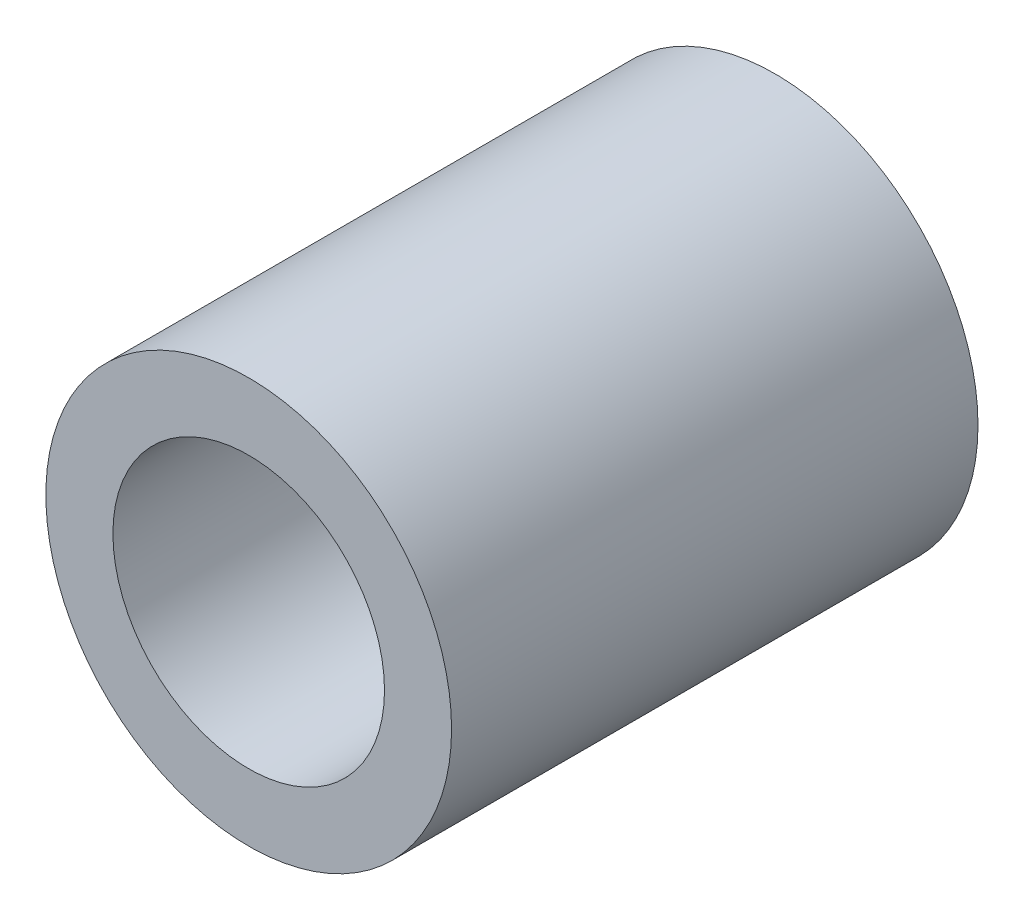
SolidWorks part; units mm, degrees
ref_plane "Alzado" through (0, 0, 0) normal (0, 0, 1) x (1, 0, 0)
ref_plane "Planta" through (0, 0, 0) normal (0, 1, 0) x (1, 0, 0)
ref_plane "Vista lateral" through (0, 0, 0) normal (1, 0, 0) x (0, 0, -1)
sketch "Croquis1" plane through (0, 0, 0) normal (0, 0, 1) x (1, 0, 0)
  circle A0 centre (0, 0) radius 4.05
  circle A1 centre (0, 0) radius 6.05
  dimension "D1" = 8.1
  dimension "D2" = 2
extrude "Saliente-Extruir1" add sketch "Croquis1" along normal blind 15.7
